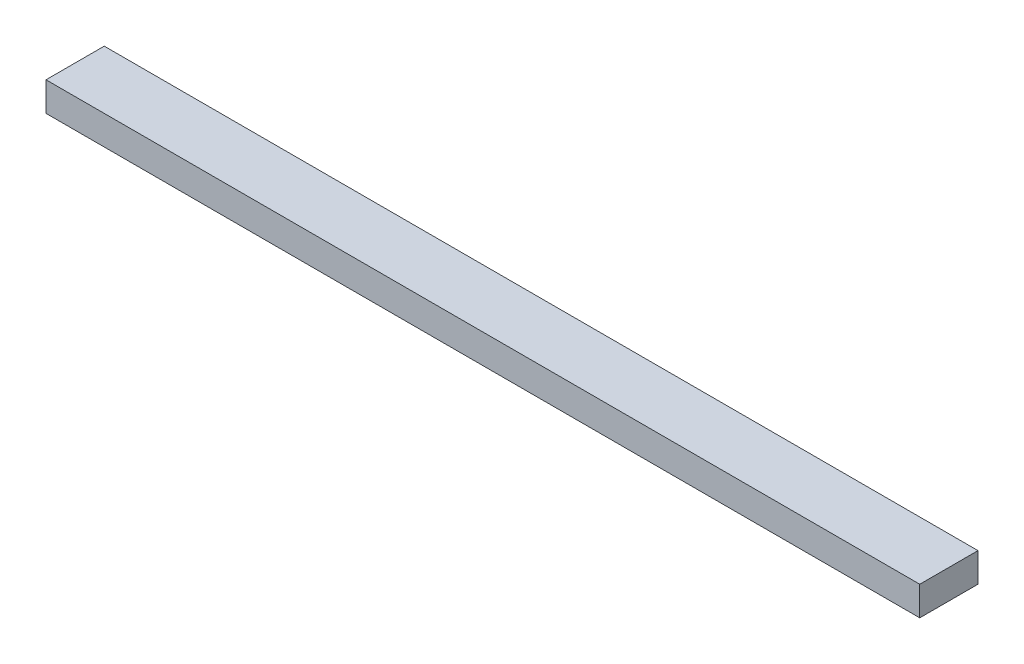
SolidWorks part; units mm, degrees
ref_plane "Alzado" through (0, 0, 0) normal (0, 0, 1) x (1, 0, 0)
ref_plane "Planta" through (0, 0, 0) normal (0, 1, 0) x (1, 0, 0)
ref_plane "Vista lateral" through (0, 0, 0) normal (1, 0, 0) x (0, 0, -1)
sketch "Croquis1" plane through (0, 0, 0) normal (0, 1, 0) x (1, 0, 0)
  line L1 (-84.0557, 15.5728) -> (65.9443, 15.5728)
  line L2 (-84.0557, 15.5728) -> (-84.0557, 5.5728)
  line L3 (-84.0557, 5.5728) -> (65.9443, 5.5728)
  line L4 (65.9443, 15.5728) -> (65.9443, 5.5728)
  dimension "D1" = 150
  dimension "D2" = 10
extrude "Saliente-Extruir1" add sketch "Croquis1" along normal blind 5
